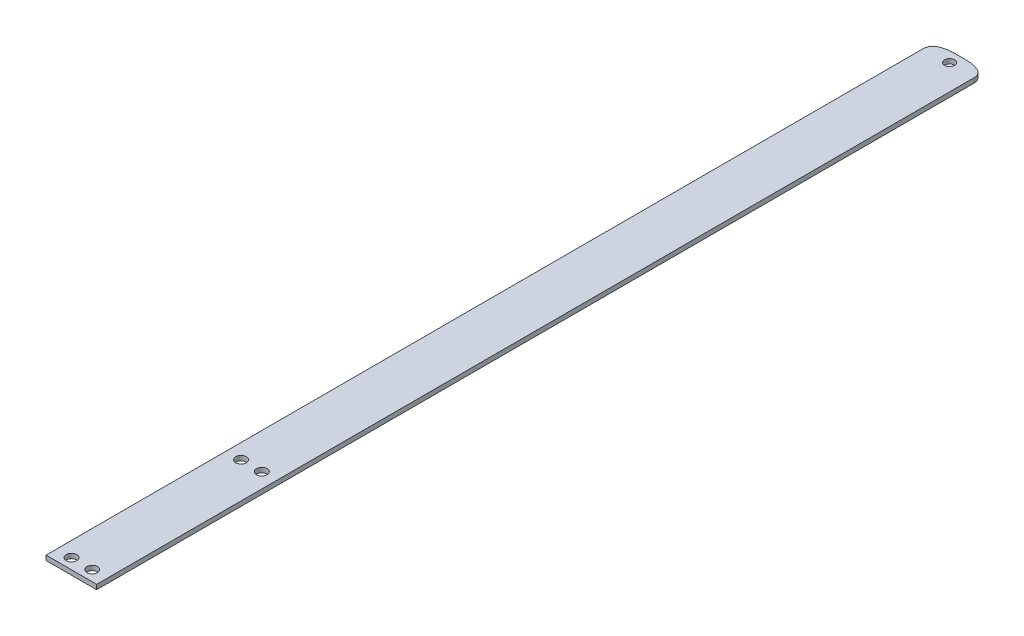
SolidWorks part; units mm, degrees
ref_plane "Front Plane" through (0, 0, 0) normal (0, 0, 1) x (1, 0, 0)
ref_plane "Top Plane" through (0, 0, 0) normal (0, 1, 0) x (1, 0, 0)
ref_plane "Right Plane" through (0, 0, 0) normal (1, 0, 0) x (0, 0, -1)
sketch "Sketch3" plane through (0, 123.7944, 0) normal (0, 1, 0) x (-1, 0, 0)
  line L10 (0, -245) -> (0, -300.54)
  line L11 (10.75, -40) -> (10.75, 70.36)
  line L20 (10.75, 70.36) -> (0, 70.36)
  line L21 (0, 70.36) -> (0, -245)
  line L25 (10.75, -40) -> (10.75, 40)
  line L26 (0, -40) -> (0, 40)
  line L27 (10.75, -40) -> (10.75, -284.4609)
  line L28 (0, -304.74) -> (0, -307.1357)
  line L31 (10.75, -284.4609) -> (10.75, -302.2952)
  line L32 (4.4, -6.14) -> (4.4, 65.86) construction
  circle A12 centre (4.4, -6.14) radius 2.25
  circle A14 centre (4.4, 65.86) radius 2.25
  arc A15 (0, -304.74) -> (0, -300.54) centre (0, -302.64) ccw
  arc A18 (10.75, -302.2952) -> (8.4702, -305.9064) centre (6.75, -302.2952) cw
  spline S0 degree 3 poles (0, -307.1357) (3.5258, -307.3265) (6.3492, -306.9167) (8.4702, -305.9064) knots 0 0 0 0 0.308955 0.308955 0.308955 0.308955
  point P32 (0, -315)
  dimension "D2" = 4
  dimension "D3" = 4.4
  dimension "D4" = 4.5
  dimension "D5" = 72
  dimension "D6" = 4.2
  dimension "D7" = 4.5
  dimension "D8" = 4.5
  dimension "D1" = 296.5
extrude "Boss-Extrude2" add sketch "Sketch3" along normal blind 2 separate body
mirror "Mirror10"
